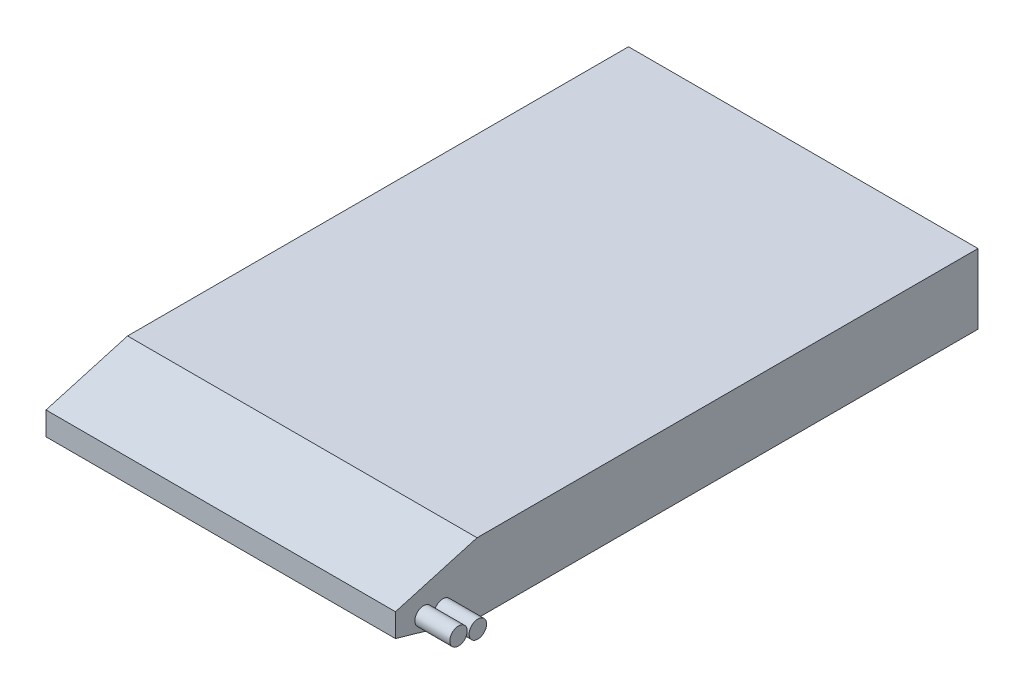
SolidWorks part; units mm, degrees
ref_plane "Front Plane" through (0, 0, 0) normal (0, 0, 1) x (1, 0, 0)
ref_plane "Top Plane" through (0, 0, 0) normal (0, 1, 0) x (1, 0, 0)
ref_plane "Right Plane" through (0, 0, 0) normal (1, 0, 0) x (0, 0, -1)
sketch "Sketch1" plane through (0, 0, 0) normal (0, 1, 0) x (1, 0, 0)
  line L0 (0, -55) -> (0, 55) construction
  line L1 (-15, 25) -> (15, 25)
  line L2 (-15, 25) -> (-15, -25)
  line L3 (-15, -25) -> (15, -25)
  line L4 (15, 25) -> (15, -25)
  line L5 (-55, 0) -> (55, 0) construction
  point P4 (0, 25)
  point P7 (15, 0)
  dimension "D1" = 50
  dimension "D2" = 30
extrude "Boss-Extrude1" add sketch "Sketch1" along normal blind 6
chamfer "Chamfer1" distance 2 distance2 7 2 edges at (0, 0, 25) (0, 6, 25)
sketch "Sketch2" plane through (15, 0, 0) normal (1, 0, 0) x (0, 0, -1)
  circle A0 centre (-22.5918, 2.492) radius 0.75
  circle A1 centre (-20.9307, 2.178) radius 0.75
  dimension "D1" = 1.5
extrude "Boss-Extrude2" add sketch "Sketch2" along normal blind 3
